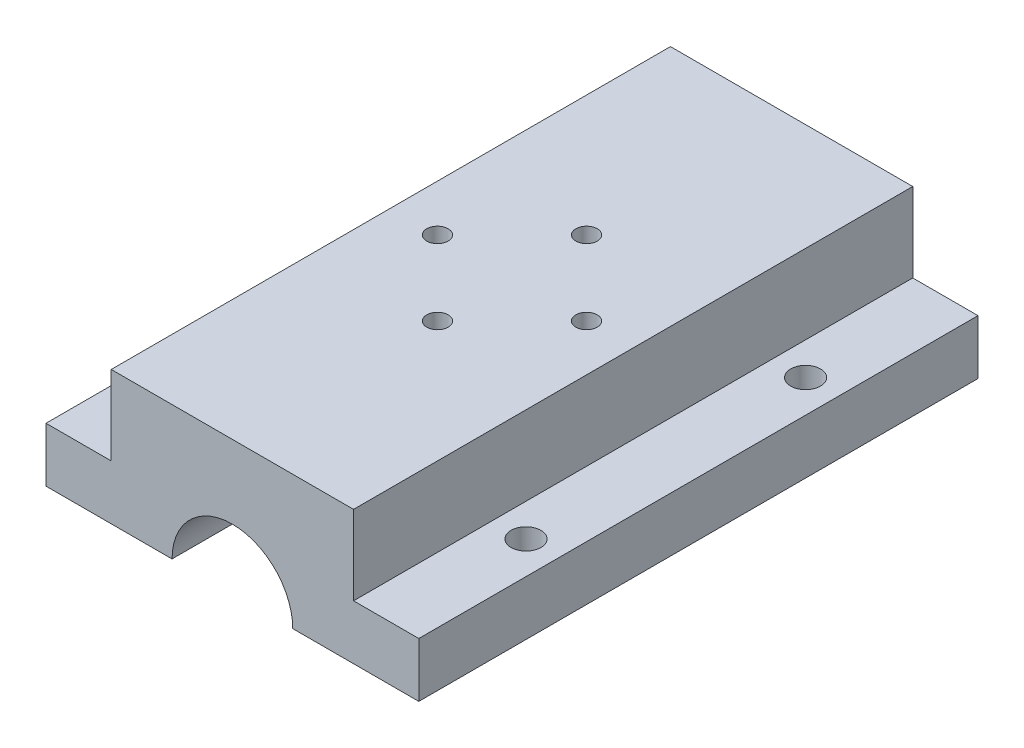
SolidWorks part; units mm, degrees
ref_plane "Front Plane" through (0, 0, 0) normal (0, 0, 1) x (1, 0, 0)
ref_plane "Top Plane" through (0, 0, 0) normal (0, 1, 0) x (1, 0, 0)
ref_plane "Right Plane" through (0, 0, 0) normal (1, 0, 0) x (0, 0, -1)
sketch "Sketch2" plane through (0, 0, 0) normal (0, 0, 1) x (1, 0, 0)
  line L0 (-6.475, 0) -> (6.475, 0) construction
  line L1 (-6.475, 0) -> (-20, 0)
  line L3 (6.475, 0) -> (20, 0)
  line L6 (-20, 0) -> (-20, 2.8476)
  line L7 (-20, 2.8476) -> (-13, 2.8476)
  line L8 (5.2286, 2.8476) -> (5.8152, 2.8476)
  line L9 (20, 2.8476) -> (20, 0)
  line L13 (-13, 2.8476) -> (-13, 14.3476)
  line L14 (-13, 14.3476) -> (13, 14.3476)
  line L15 (13, 14.3476) -> (13, 2.8476)
  line L16 (13, 2.8476) -> (20, 2.8476)
  arc A0 (6.475, 0) -> (-6.475, 0) centre (0, 0) ccw
  dimension "D1" = 6.475
  dimension "D6" = 11.5
  dimension "D2" = 13
  dimension "D3" = 7
  dimension "D4" = 13
  dimension "D5" = 7
extrude "Boss-Extrude6" add sketch "Sketch2" along normal blind 60 contours A0 L3 L9 L16 L15 L14 L13 L7 L6 L1
ref_plane "Plane4" through (0, 2.8476, 0) normal (0, 1, 0) x (1, 0, 0)
sketch "Sketch9" plane through (0, 2.8476, 0) normal (0, 1, 0) x (1, 0, 0)
  circle A0 centre (-16.5, -15) radius 1.6
  circle A1 centre (-16.5, -45) radius 1.6
  circle A2 centre (16.5, -15) radius 1.6
  circle A3 centre (16.5, -45) radius 1.6
  dimension "D1" = 3.2
  dimension "D2" = 3.2
  dimension "D3" = 3.2
  dimension "D4" = 3.2
extrude "Cut-Extrude3" cut sketch "Sketch9" against normal blind 50
ref_plane "Plane5" through (0, 14.3476, 0) normal (0, 1, 0) x (1, 0, 0)
sketch "Sketch10" plane through (0, 14.3476, 0) normal (0, 1, 0) x (1, 0, 0)
  line L0 (0, 0) -> (0, -30) construction
  circle A4 centre (0, -22) radius 1.15
  circle A5 centre (8, -30) radius 1.15
  circle A6 centre (-8, -30) radius 1.15
  circle A7 centre (0, -38) radius 1.15
  dimension "D4" = 2.3
  dimension "D5" = 8
  dimension "D7" = 8
  dimension "D2" = 2.3
  dimension "D6" = 2.3
  dimension "D8" = 2.3
  dimension "D1" = 8
  dimension "D3" = 8
extrude "Cut-Extrude5" cut sketch "Sketch10" against normal blind 22.05
ref_plane "Plane6" through (0, 2.8476, 0) normal (0, 1, 0) x (1, 0, 0)
sketch "Sketch11" plane through (0, 2.8476, 0) normal (0, 1, 0) x (1, 0, 0)
  line L0 (20, -60) -> (20, 0)
  line L1 (20, 0) -> (13, 0)
  line L2 (13, 0) -> (13, -60)
  line L3 (13, -60) -> (20, -60)
  circle A0 centre (16.5, -45) radius 1.6
  circle A1 centre (16.5, -15) radius 1.6
extrude "Boss-Extrude7" add sketch "Sketch11" along normal blind 3
sketch "Sketch12" plane through (0, 2.8476, 0) normal (0, 1, 0) x (1, 0, 0)
  line L0 (-20, -60) -> (-13, -60)
  line L1 (-20, -60) -> (-13, -60) construction
  line L2 (-13, -60) -> (-13, 0)
  line L3 (-13, 0) -> (-20, 0)
  line L4 (-20, 0) -> (-20, -60)
  circle A0 centre (-16.5, -45) radius 1.6
  circle A1 centre (-16.5, -15) radius 1.6
extrude "Boss-Extrude8" add sketch "Sketch12" along normal blind 3
ref_plane "Plane8" through (0, 0, 0) normal (0, -1, 0) x (-1, 0, 0)
sketch "Sketch16" plane through (0, 0, 0) normal (0, -1, 0) x (-1, 0, 0)
  circle A0 centre (0, -22) radius 2.5
  circle A1 centre (0, -38) radius 2.5
  dimension "D1" = 5
  dimension "D2" = 5
extrude "Cut-Extrude9" cut sketch "Sketch16" against normal blind 8.75
sketch "Sketch17" plane through (0, 0, 0) normal (0, -1, 0) x (-1, 0, 0)
  circle A0 centre (-8, -30) radius 2.5
  circle A1 centre (8, -30) radius 2.5
  dimension "5" = 5
  dimension "D2" = 5
extrude "Cut-Extrude10" cut sketch "Sketch17" against normal blind 8.75
